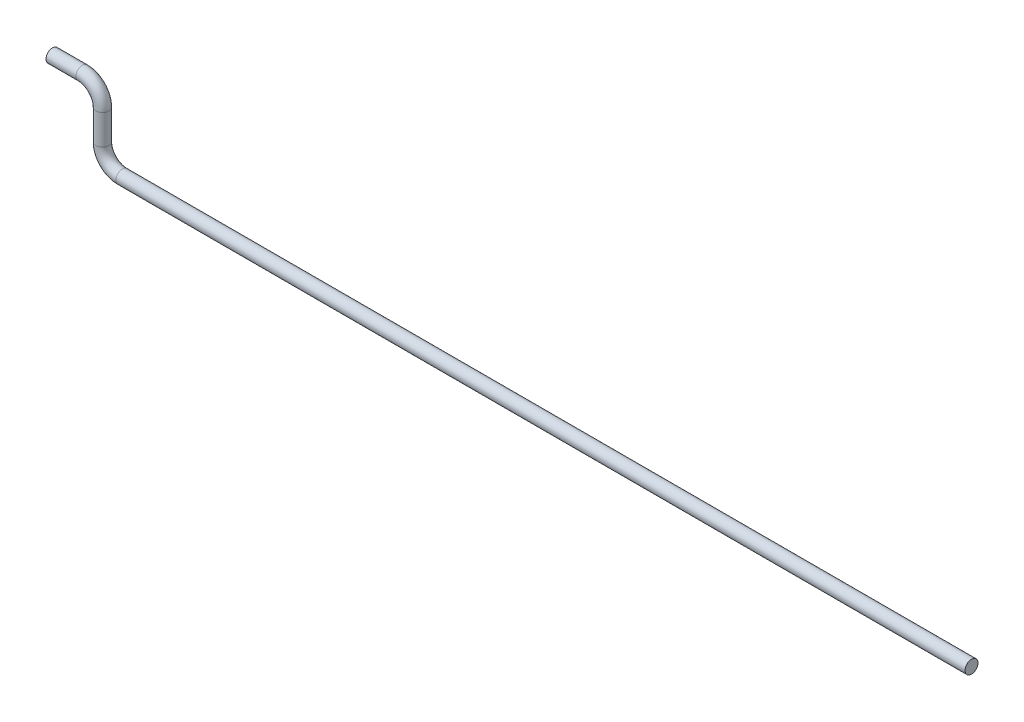
SolidWorks part; units mm, degrees
ref_plane "Front Plane" through (0, 0, 0) normal (0, 0, 1) x (1, 0, 0)
ref_plane "Top Plane" through (0, 0, 0) normal (0, 1, 0) x (1, 0, 0)
ref_plane "Right Plane" through (0, 0, 0) normal (1, 0, 0) x (0, 0, -1)
sketch "Sketch1" plane through (0, 0, 0) normal (0, 0, 1) x (1, 0, 0)
  line L0 (0, 0) -> (85, 0)
  line L1 (-2, 2) -> (-2, 5)
  line L2 (-4, 7) -> (-7, 7)
  arc A0 (0, 0) -> (-2, 2) centre (0, 2) cw
  arc A1 (-2, 5) -> (-4, 7) centre (-4, 5) ccw
  dimension "D2" = 2
  dimension "D3" = 2
  dimension "D1" = 85
  dimension "D4" = 3
  dimension "D5" = 3
ref_plane "Plane1" through (85, 0, 0) normal (1, 0, 0) x (0, 0, -1)
sketch "Sketch2" plane through (85, 0, 0) normal (1, 0, 0) x (0, 0, -1)
  circle A0 centre (0, 0) radius 0.65
  dimension "D1" = 1.3
sweep "Sweep1" add profiles "Sketch2" path "Sketch1"
